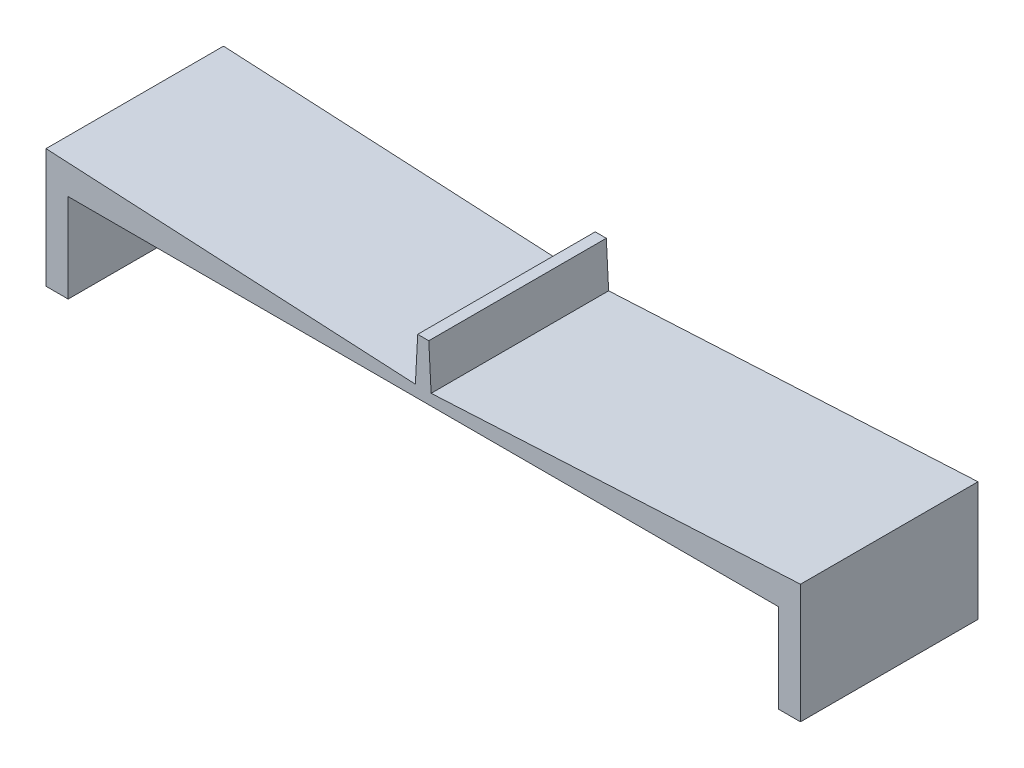
SolidWorks part; units mm, degrees
ref_plane "Front Plane" through (0, 0, 0) normal (0, 0, 1) x (1, 0, 0)
ref_plane "Top Plane" through (0, 0, 0) normal (0, 1, 0) x (1, 0, 0)
ref_plane "Right Plane" through (0, 0, 0) normal (1, 0, 0) x (0, 0, -1)
sketch "Sketch3" plane through (0, 0, 0) normal (0, 0, 1) x (1, 0, 0)
  line L0 (0, 1.5875) -> (0, 7.9375)
  line L1 (0, 0) -> (53.975, 0)
  line L2 (0, 0) -> (0, 1.5875)
  line L3 (0, 1.5875) -> (53.975, 1.5875)
  line L4 (53.975, 0) -> (53.975, 1.5875)
  line L5 (53.975, 0) -> (50.8, 0)
  line L6 (53.975, 0) -> (53.975, -12.7)
  line L7 (53.975, -12.7) -> (50.8, -12.7)
  line L8 (50.8, 0) -> (50.8, -12.7)
  line L9 (0.7937, 7.9375) -> (1.1265, 1.5875)
  line L10 (1.1265, 1.5875) -> (53.975, 4.3572)
  line L11 (53.975, 4.3572) -> (53.975, 1.5875)
  line L12 (0, 7.9375) -> (0.7937, 7.9375)
  dimension "D1" = 1.5875
  dimension "D2" = 50.8
  dimension "D3" = 12.7
  dimension "D4" = 3.175
  dimension "D5" = 3
  dimension "D6" = 0.7937
  dimension "D7" = 6.35
extrude "Boss-Extrude2" add sketch "Sketch3" along normal blind 25.4 contours L1 L4 L3 L2 | L1 L8 L7 L6 | L11 L10 L3 | L12 L0 L3 L9
mirror "Mirror1" about plane through (0, 0, 0) normal (1, 0, 0) of "Boss-Extrude2"
